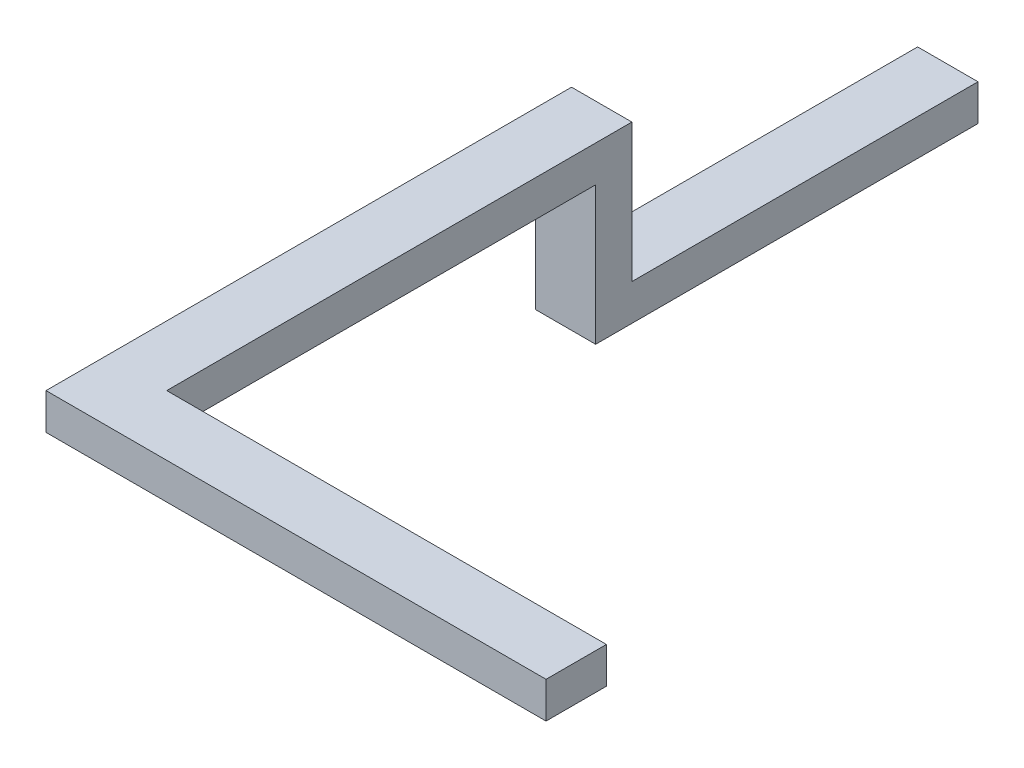
SolidWorks part; units mm, degrees
ref_plane "Front Plane" through (0, 0, 0) normal (0, 0, 1) x (1, 0, 0)
ref_plane "Top Plane" through (0, 0, 0) normal (0, 1, 0) x (1, 0, 0)
ref_plane "Right Plane" through (0, 0, 0) normal (1, 0, 0) x (0, 0, -1)
sketch "Sketch1" plane through (0, 0, 0) normal (0, 0, 1) x (1, 0, 0)
  line L1 (-900, 540) -> (0, 540)
  line L2 (-900, 540) -> (-900, 0)
  line L3 (-900, 0) -> (0, 0)
  line L4 (0, 540) -> (0, 0)
  dimension "D1" = 900
  dimension "D2" = 540
sketch "Sketch2" plane through (0, 0, 0) normal (1, 0, 0) x (0, 0, -1)
  line L0 (0, 270) -> (-5430, 270)
  line L1 (0, 540) -> (0, 0) construction
  line L2 (-5430, 270) -> (-5430, 2330)
  line L3 (-5430, 2330) -> (-12995, 2330)
  dimension "D1" = 7565
  dimension "D2" = 5430
  dimension "D3" = 2060
sweep "Sweep1" add profiles "Sketch1" path "Sketch2"
sketch "Sketch4" plane through (0, 0, 0) normal (1, 0, 0) x (0, 0, -1)
  line L0 (-5160, 2600) -> (-12995, 2600) construction
  line L1 (-12995, 2060) -> (-12095, 2060)
  line L2 (-12995, 2060) -> (-12995, 2600)
  line L3 (-12995, 2600) -> (-12095, 2600)
  line L4 (-12095, 2060) -> (-12095, 2600)
  dimension "D1" = 900
extrude "Boss-Extrude1" add sketch "Sketch4" along normal blind 6555
